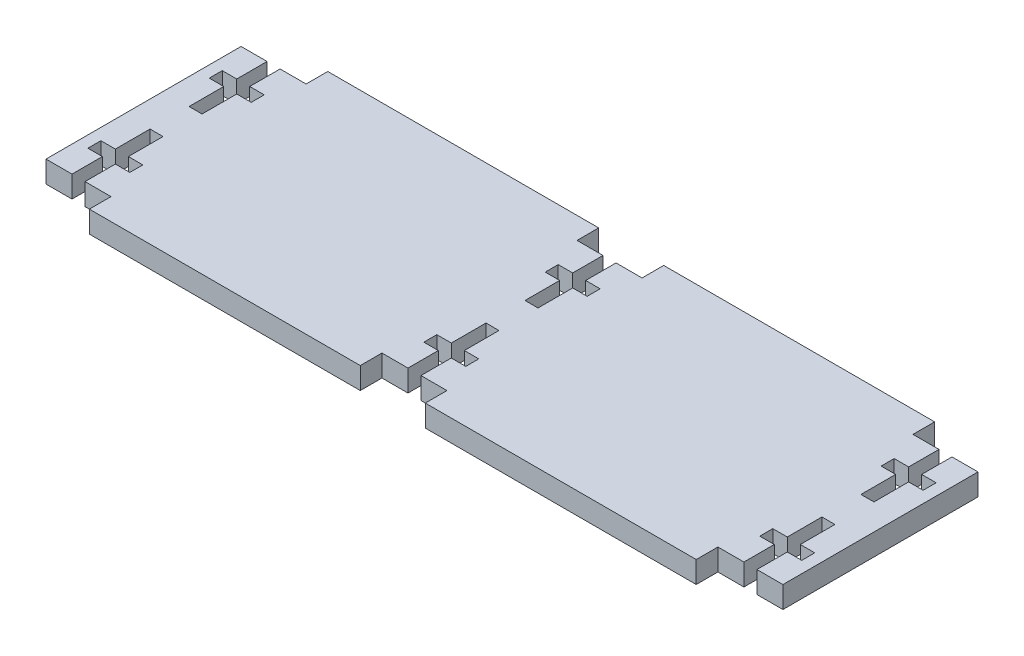
SolidWorks part; units mm, degrees
material "PVC rigido"
ref_plane "Piano frontale" through (0, 0, 0) normal (0, 0, 1) x (1, 0, 0)
ref_plane "Piano superiore" through (0, 0, 0) normal (0, 1, 0) x (1, 0, 0)
ref_plane "Piano destro" through (0, 0, 0) normal (1, 0, 0) x (0, 0, -1)
sketch "Schizzo1" plane through (0, 0, 0) normal (0, 1, 0) x (1, 0, 0)
  line L1 (-54.5649, -28.2811) -> (115.4351, -28.2811)
  line L2 (-54.5649, -28.2811) -> (-54.5649, 26.7189)
  line L3 (-54.5649, 26.7189) -> (115.4351, 26.7189)
  line L4 (115.4351, -28.2811) -> (115.4351, 26.7189)
  dimension "D1" = 170
  dimension "D2" = 55
sketch "Schizzo2" plane through (0, 0, 0) normal (0, 1, 0) x (1, 0, 0)
  line L0 (-54.5649, -0.7811) -> (115.4351, -0.7811) construction
  line L1 (-54.5649, -28.2811) -> (-39.5649, -28.2811)
  line L2 (-54.5649, -28.2811) -> (-54.5649, -23.2811)
  line L3 (-54.5649, -23.2811) -> (-39.5649, -23.2811)
  line L4 (-39.5649, -28.2811) -> (-39.5649, -23.2811)
  line L5 (-54.5649, -28.2811) -> (-54.5649, 26.7189) construction
  line L6 (115.4351, -28.2811) -> (115.4351, 26.7189) construction
  line L7 (30.4351, -28.2811) -> (30.4351, 26.7189) construction
  line L8 (-54.5649, -28.2811) -> (115.4351, -28.2811) construction
  line L9 (-54.5649, 26.7189) -> (115.4351, 26.7189) construction
  line L10 (-54.5649, 26.7189) -> (-54.5649, 21.7189)
  line L11 (-54.5649, 26.7189) -> (-39.5649, 26.7189)
  line L12 (-39.5649, 26.7189) -> (-39.5649, 21.7189)
  line L13 (-54.5649, 21.7189) -> (-39.5649, 21.7189)
  line L14 (115.4351, -28.2811) -> (115.4351, -23.2811)
  line L15 (115.4351, -28.2811) -> (100.4351, -28.2811)
  line L16 (100.4351, -28.2811) -> (100.4351, -23.2811)
  line L17 (115.4351, -23.2811) -> (100.4351, -23.2811)
  line L18 (115.4351, 26.7189) -> (115.4351, 21.7189)
  line L19 (115.4351, 26.7189) -> (100.4351, 26.7189)
  line L20 (100.4351, 26.7189) -> (100.4351, 21.7189)
  line L21 (115.4351, 21.7189) -> (100.4351, 21.7189)
  line L22 (22.9351, -28.2811) -> (37.9351, -28.2811)
  line L23 (22.9351, -28.2811) -> (22.9351, -23.2811)
  line L24 (22.9351, -23.2811) -> (37.9351, -23.2811)
  line L25 (37.9351, -28.2811) -> (37.9351, -23.2811)
  line L26 (22.9351, 26.7189) -> (22.9351, 21.7189)
  line L27 (22.9351, 21.7189) -> (37.9351, 21.7189)
  line L28 (37.9351, 26.7189) -> (37.9351, 21.7189)
  line L29 (22.9351, 26.7189) -> (37.9351, 26.7189)
  point P33 (30.4351, -23.2811)
  dimension "D1" = 15
  dimension "D2" = 5
  dimension "D3" = 15
  dimension "D4" = 5
extrude "Estrusione-Estrusione2" add sketch "Schizzo1" against normal blind 5
extrude "Taglio-Estrusione1" cut sketch "Schizzo2" against normal through all
sketch "Schizzo3" plane through (0, 0, 0) normal (0, 1, 0) x (1, 0, 0)
  line L0 (-48.5649, -23.2811) -> (-45.5649, -23.2811)
  line L1 (28.9351, -23.2811) -> (31.9351, -23.2811)
  line L2 (-54.5649, -0.7811) -> (115.4351, -0.7811) construction
  line L3 (-54.5649, 21.7189) -> (-54.5649, -23.2811) construction
  line L4 (-48.5649, -23.2811) -> (-48.5649, -16.2811)
  line L5 (-48.5649, -16.2811) -> (-51.9049, -16.2811)
  line L6 (-51.9049, -16.2811) -> (-51.9049, -13.2811)
  line L7 (-51.9049, -13.2811) -> (-48.5649, -13.2811)
  line L8 (-48.5649, -13.2811) -> (-48.5649, -5.2811)
  line L9 (-48.5649, -5.2811) -> (-45.5649, -5.2811)
  line L10 (-45.5649, -5.2811) -> (-45.5649, -13.2811)
  line L11 (-45.5649, -13.2811) -> (-42.2249, -13.2811)
  line L12 (-42.2249, -13.2811) -> (-42.2249, -16.2811)
  line L13 (-42.2249, -16.2811) -> (-45.5649, -16.2811)
  line L14 (-45.5649, -16.2811) -> (-45.5649, -23.2811)
  line L15 (115.4351, -23.2811) -> (115.4351, 21.7189) construction
  line L16 (-47.0649, 21.7189) -> (-47.0649, -23.2811) construction
  line L17 (-54.5649, 21.7189) -> (-39.5649, 21.7189) construction
  line L18 (-39.5649, -23.2811) -> (-54.5649, -23.2811) construction
  line L19 (30.4351, 21.7189) -> (30.4351, -23.2811) construction
  line L20 (22.9351, 21.7189) -> (37.9351, 21.7189) construction
  line L21 (37.9351, -23.2811) -> (22.9351, -23.2811) construction
  line L22 (107.9351, 21.7189) -> (107.9351, -23.2811) construction
  line L23 (100.4351, 21.7189) -> (115.4351, 21.7189) construction
  line L24 (115.4351, -23.2811) -> (100.4351, -23.2811) construction
  line L25 (106.4351, -23.2811) -> (109.4351, -23.2811)
  line L26 (28.9351, -23.2811) -> (28.9351, -16.2811)
  line L27 (28.9351, -16.2811) -> (25.5951, -16.2811)
  line L28 (25.5951, -16.2811) -> (25.5951, -13.2811)
  line L29 (25.5951, -13.2811) -> (28.9351, -13.2811)
  line L30 (28.9351, -13.2811) -> (28.9351, -5.2811)
  line L31 (28.9351, -5.2811) -> (31.9351, -5.2811)
  line L32 (31.9351, -5.2811) -> (31.9351, -13.2811)
  line L33 (31.9351, -13.2811) -> (35.2751, -13.2811)
  line L34 (35.2751, -13.2811) -> (35.2751, -16.2811)
  line L35 (35.2751, -16.2811) -> (31.9351, -16.2811)
  line L36 (31.9351, -16.2811) -> (31.9351, -23.2811)
  line L37 (106.4351, 3.7189) -> (109.4351, 3.7189)
  line L38 (106.4351, -23.2811) -> (106.4351, -16.2811)
  line L39 (106.4351, -16.2811) -> (103.0951, -16.2811)
  line L40 (103.0951, -16.2811) -> (103.0951, -13.2811)
  line L41 (103.0951, -13.2811) -> (106.4351, -13.2811)
  line L42 (106.4351, -13.2811) -> (106.4351, -5.2811)
  line L43 (106.4351, -5.2811) -> (109.4351, -5.2811)
  line L44 (109.4351, -5.2811) -> (109.4351, -13.2811)
  line L45 (109.4351, -13.2811) -> (112.7751, -13.2811)
  line L46 (112.7751, -13.2811) -> (112.7751, -16.2811)
  line L47 (112.7751, -16.2811) -> (109.4351, -16.2811)
  line L48 (109.4351, -16.2811) -> (109.4351, -23.2811)
  line L49 (106.4351, 11.7189) -> (106.4351, 3.7189)
  line L50 (103.0951, 11.7189) -> (106.4351, 11.7189)
  line L51 (103.0951, 14.7189) -> (103.0951, 11.7189)
  line L52 (106.4351, 14.7189) -> (103.0951, 14.7189)
  line L53 (106.4351, 21.7189) -> (106.4351, 14.7189)
  line L54 (106.4351, 21.7189) -> (109.4351, 21.7189)
  line L55 (109.4351, 14.7189) -> (109.4351, 21.7189)
  line L56 (112.7751, 14.7189) -> (109.4351, 14.7189)
  line L57 (112.7751, 11.7189) -> (112.7751, 14.7189)
  line L58 (109.4351, 11.7189) -> (112.7751, 11.7189)
  line L59 (109.4351, 3.7189) -> (109.4351, 11.7189)
  line L60 (28.9351, 3.7189) -> (31.9351, 3.7189)
  line L61 (28.9351, 11.7189) -> (28.9351, 3.7189)
  line L62 (25.5951, 11.7189) -> (28.9351, 11.7189)
  line L63 (25.5951, 14.7189) -> (25.5951, 11.7189)
  line L64 (28.9351, 14.7189) -> (25.5951, 14.7189)
  line L65 (28.9351, 21.7189) -> (28.9351, 14.7189)
  line L66 (28.9351, 21.7189) -> (31.9351, 21.7189)
  line L67 (31.9351, 14.7189) -> (31.9351, 21.7189)
  line L68 (35.2751, 14.7189) -> (31.9351, 14.7189)
  line L69 (35.2751, 11.7189) -> (35.2751, 14.7189)
  line L70 (31.9351, 11.7189) -> (35.2751, 11.7189)
  line L71 (31.9351, 3.7189) -> (31.9351, 11.7189)
  line L72 (-48.5649, 3.7189) -> (-45.5649, 3.7189)
  line L73 (-48.5649, 11.7189) -> (-48.5649, 3.7189)
  line L74 (-51.9049, 11.7189) -> (-48.5649, 11.7189)
  line L75 (-51.9049, 14.7189) -> (-51.9049, 11.7189)
  line L76 (-48.5649, 14.7189) -> (-51.9049, 14.7189)
  line L77 (-48.5649, 21.7189) -> (-48.5649, 14.7189)
  line L78 (-48.5649, 21.7189) -> (-45.5649, 21.7189)
  line L79 (-45.5649, 14.7189) -> (-45.5649, 21.7189)
  line L80 (-42.2249, 14.7189) -> (-45.5649, 14.7189)
  line L81 (-42.2249, 11.7189) -> (-42.2249, 14.7189)
  line L82 (-45.5649, 11.7189) -> (-42.2249, 11.7189)
  line L83 (-45.5649, 3.7189) -> (-45.5649, 11.7189)
  point P36 (-47.0649, -23.2811)
  point P53 (30.4351, -23.2811)
  point P66 (107.9351, -23.2811)
  dimension "D1" = 8
  dimension "D2" = 3
  dimension "D3" = 3
  dimension "D4" = 7
  dimension "D5" = 3.34
  dimension "D6" = 77.5
  dimension "D7" = 77.5
  dimension "D8" = 3
  dimension "D9" = 7
  dimension "D10" = 8
  dimension "D11" = 3
  dimension "D12" = 3.34
  dimension "D13" = 3
  dimension "D14" = 7
  dimension "D15" = 8
  dimension "D16" = 3
  dimension "D17" = 3.34
extrude "Taglio-Estrusione3" cut sketch "Schizzo3" against normal through all
